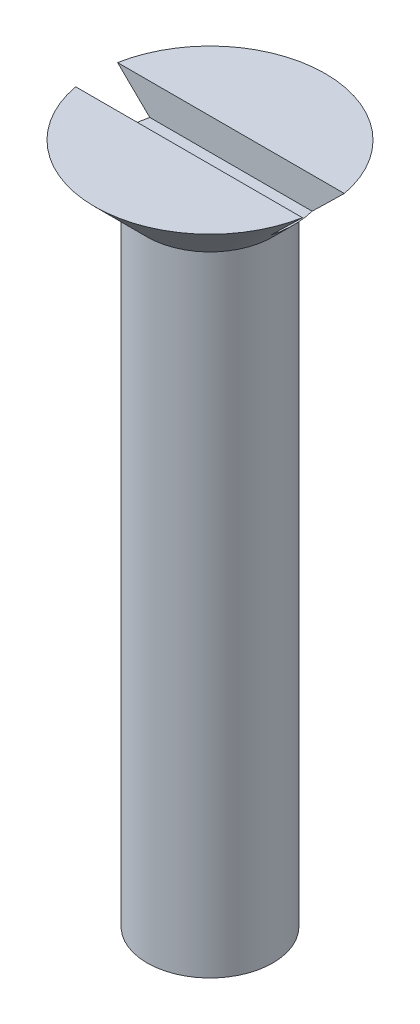
SolidWorks part; units mm, degrees
ref_plane "Front Plane" through (0, 0, 0) normal (0, 0, 1) x (1, 0, 0)
ref_plane "Top Plane" through (0, 0, 0) normal (0, 1, 0) x (1, 0, 0)
ref_plane "Right Plane" through (0, 0, 0) normal (1, 0, 0) x (0, 0, -1)
sketch "Sketch1" plane through (0, 0, 0) normal (1, 0, 0) x (0, 0, -1)
  line L0 (0, 0) -> (-1.5, 0)
  line L1 (-1.5, 0) -> (-1.5, 15)
  line L2 (-1.5, 15) -> (-2.75, 16.25)
  line L3 (-2.75, 16.25) -> (0, 16.25)
  line L4 (0, 16.25) -> (0, 0)
  dimension "D1" = 1.5
  dimension "D2" = 45
  dimension "D3" = 2.75
  dimension "D4" = 15
revolve "Revolve1" add sketch "Sketch1" angle 360 about L4
sketch "Sketch2" plane through (0, 16.25, 0) normal (0, 1, 0) x (1, 0, 0)
  line L0 (0, 0) -> (0, 0.5) construction
  line L1 (-2.75, 0.5) -> (2.75, 0.5)
  line L2 (-2.75, 0.5) -> (-2.75, -0.5)
  line L3 (-2.75, -0.5) -> (2.75, -0.5)
  line L4 (2.75, 0.5) -> (2.75, -0.5)
  line L5 (-2.75, 0) -> (0, 0) construction
  circle A0 centre (0, 0) radius 2.75 construction
  dimension "D1" = 1
extrude "Cut-Extrude1" cut sketch "Sketch2" against normal blind 0.75
